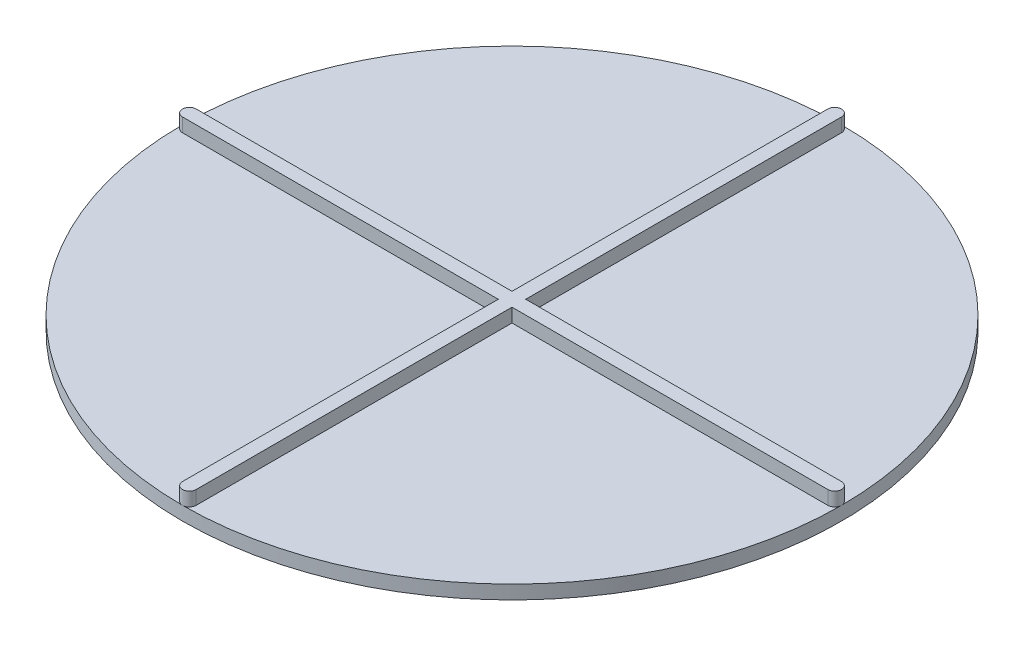
SolidWorks part; units mm, degrees
ref_plane "Front Plane" through (0, 0, 0) normal (0, 0, 1) x (1, 0, 0)
ref_plane "Top Plane" through (0, 0, 0) normal (0, 1, 0) x (1, 0, 0)
ref_plane "Right Plane" through (0, 0, 0) normal (1, 0, 0) x (0, 0, -1)
sketch "Sketch1" plane through (0, 0, 0) normal (0, 1, 0) x (1, 0, 0)
  circle A0 centre (0, 0) radius 76.2
  dimension "D1" = 152.4
extrude "Boss-Extrude1" add sketch "Sketch1" along normal blind 3.175
sketch "Sketch2" plane through (0, 3.175, 0) normal (0, 1, 0) x (1, 0, 0)
  line L0 (0, -76.2) -> (0, 76.2)
  line L1 (-76.2, 0) -> (76.2, 0)
  line L2 (-74.6125, 0) -> (74.6125, 0) construction
  line L3 (-74.6125, 1.5875) -> (74.6125, 1.5875)
  line L4 (-74.6125, -1.5875) -> (74.6125, -1.5875)
  line L5 (0, 74.6125) -> (0, -74.6125) construction
  line L6 (1.5875, 74.6125) -> (1.5875, -74.6125)
  line L7 (-1.5875, 74.6125) -> (-1.5875, -74.6125)
  circle A0 centre (0, 0) radius 76.2 construction
  arc A1 (-74.6125, 1.5875) -> (-74.6125, -1.5875) centre (-74.6125, 0) ccw
  arc A2 (74.6125, -1.5875) -> (74.6125, 1.5875) centre (74.6125, 0) ccw
  arc A3 (1.5875, 74.6125) -> (-1.5875, 74.6125) centre (0, 74.6125) ccw
  arc A4 (-1.5875, -74.6125) -> (1.5875, -74.6125) centre (0, -74.6125) ccw
  point P7 (0, 0)
  point P11 (0, 0)
  point P12 (0, 0)
  point P19 (0, 0)
  dimension "D1" = 3.175
  dimension "D2" = 3.175
extrude "Boss-Extrude2" add sketch "Sketch2" along normal blind 3.175 contours L7 A4 L6 A3 | L4 A1 L3 A2
